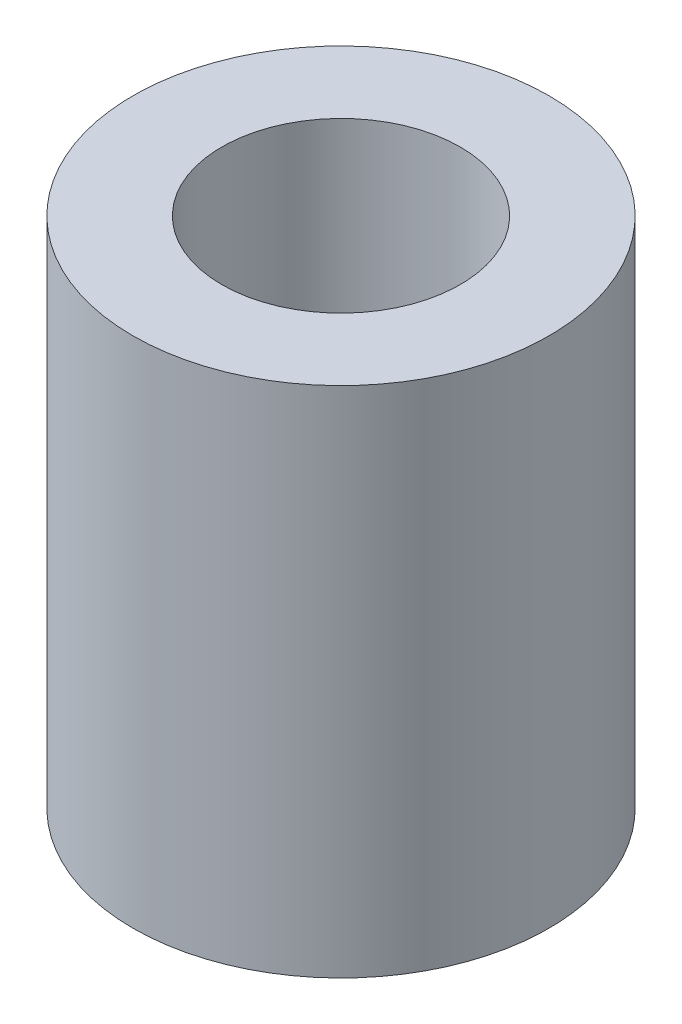
SolidWorks part; units mm, degrees
material "ABS"
ref_plane "Front Plane" through (0, 0, 0) normal (0, 0, 1) x (1, 0, 0)
ref_plane "Top Plane" through (0, 0, 0) normal (0, 1, 0) x (1, 0, 0)
ref_plane "Right Plane" through (0, 0, 0) normal (1, 0, 0) x (0, 0, -1)
sketch "Sketch1" plane through (0, 0, 0) normal (0, 1, 0) x (1, 0, 0)
  circle A0 centre (0, 0) radius 2.7305
  circle A1 centre (0, 0) radius 4.7625
  dimension "D1" = 5.461
  dimension "D2" = 9.525
extrude "Boss-Extrude1" add sketch "Sketch1" along normal blind 11.7475
